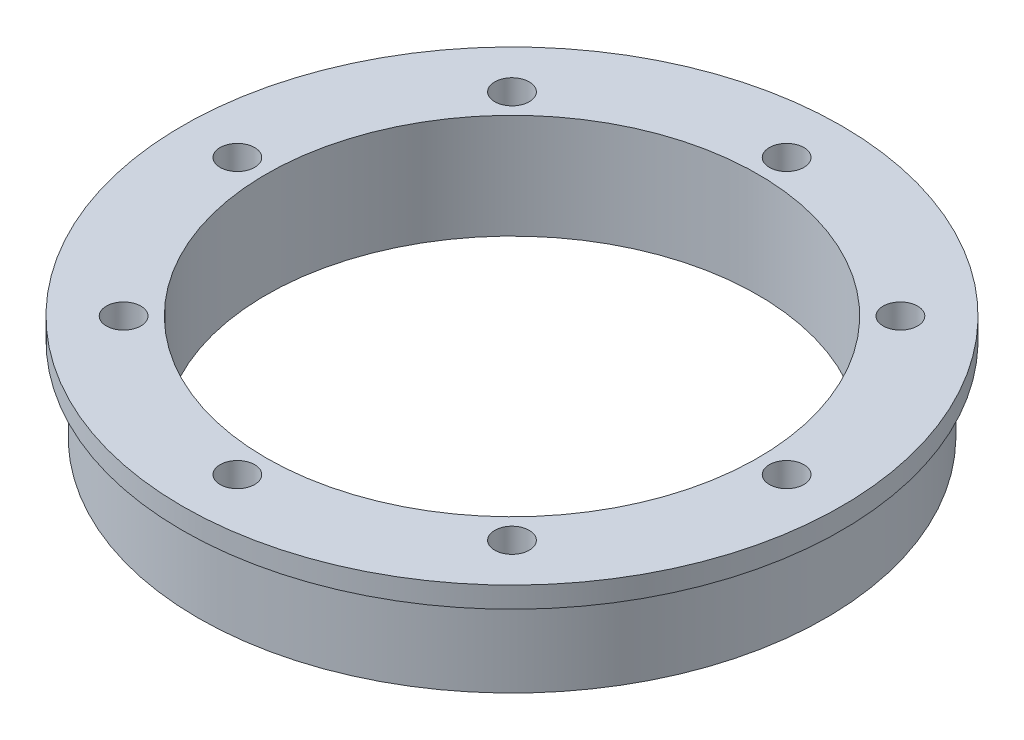
SolidWorks part; units mm, degrees
material "1060 合金"
ref_plane "前视基准面" through (0, 0, 0) normal (0, 0, 1) x (1, 0, 0)
ref_plane "上视基准面" through (0, 0, 0) normal (0, 1, 0) x (1, 0, 0)
ref_plane "右视基准面" through (0, 0, 0) normal (1, 0, 0) x (0, 0, -1)
other "Configuration Table"
sketch "草图1" plane through (0, 0, 0) normal (0, 1, 0) x (1, 0, 0)
  circle A0 centre (0, 0) radius 23.5
  circle A1 centre (0, 0) radius 30
  dimension "D1" = 60
  dimension "D2" = 47
extrude "凸台-拉伸1" add sketch "草图1" along normal blind 10
sketch "草图2" plane through (0, 10, 0) normal (0, 1, 0) x (1, 0, 0)
  circle A0 centre (0, 0) radius 30
  circle A1 centre (0, 0) radius 31.5
  dimension "D1" = 63
  dimension "D2" = 60
extrude "凸台-拉伸2" add sketch "草图2" against normal blind 2
sketch "草图3" plane through (0, 0, 0) normal (0, -1, 0) x (1, 0, 0)
  circle A0 centre (0, 0) radius 26.25 construction
  circle A1 centre (0, 26.25) radius 1.775
  circle A2 centre (18.5616, 18.5616) radius 1.775
  circle A3 centre (26.25, 0) radius 1.775
  circle A4 centre (18.5616, -18.5616) radius 1.775
  circle A5 centre (0, -26.25) radius 1.775
  circle A6 centre (-18.5616, -18.5616) radius 1.775
  circle A7 centre (-26.25, 0) radius 1.775
  circle A8 centre (-18.5616, 18.5616) radius 1.775
  point P21 (0, 0)
  dimension "D1" = 52.5
  dimension "D2" = 3.55
  dimension "D3" = 8
hole_wizard "M4 螺纹孔1" positions "3D草图1" profile "草图4" tap size "M4" standard "GB" end condition through all
sketch3d "3D草图1"
  point P0 (-18.5616, 0, 18.5616)
  point P3 (0, 0, 26.25)
  point P6 (-26.25, 0, 0)
  point P9 (-18.5616, 0, -18.5616)
  point P12 (0, 0, -26.25)
  point P15 (18.5616, 0, -18.5616)
  point P18 (26.25, 0, 0)
  point P21 (18.5616, 0, 18.5616)
sketch "草图4" plane through (-18.5616, 0, 18.5616) normal (1, 0, 0) x (0, 0, -1)
  line L0 (0, 0) -> (0, 10)
  line L1 (0, 10) -> (1.65, 10)
  line L2 (1.65, 10) -> (1.65, 0)
  line L5 (1.65, 0) -> (0, 0)
  line L11 (0, -6.35) -> (0, 107.95) construction
  dimension "通孔螺纹孔钻头直径" = 3.3
  dimension "通孔螺纹孔钻头深度" = 10
cosmetic thread "孔螺蚊线1" parameters "D2"=4
cosmetic thread "孔螺蚊线2" parameters "D2"=4
cosmetic thread "孔螺蚊线3" parameters "D2"=4
cosmetic thread "孔螺蚊线4" parameters "D2"=4
cosmetic thread "孔螺蚊线5" parameters "D2"=4
cosmetic thread "孔螺蚊线6" parameters "D2"=4
cosmetic thread "孔螺蚊线7" parameters "D2"=4
cosmetic thread "孔螺蚊线8" parameters "D2"=4
